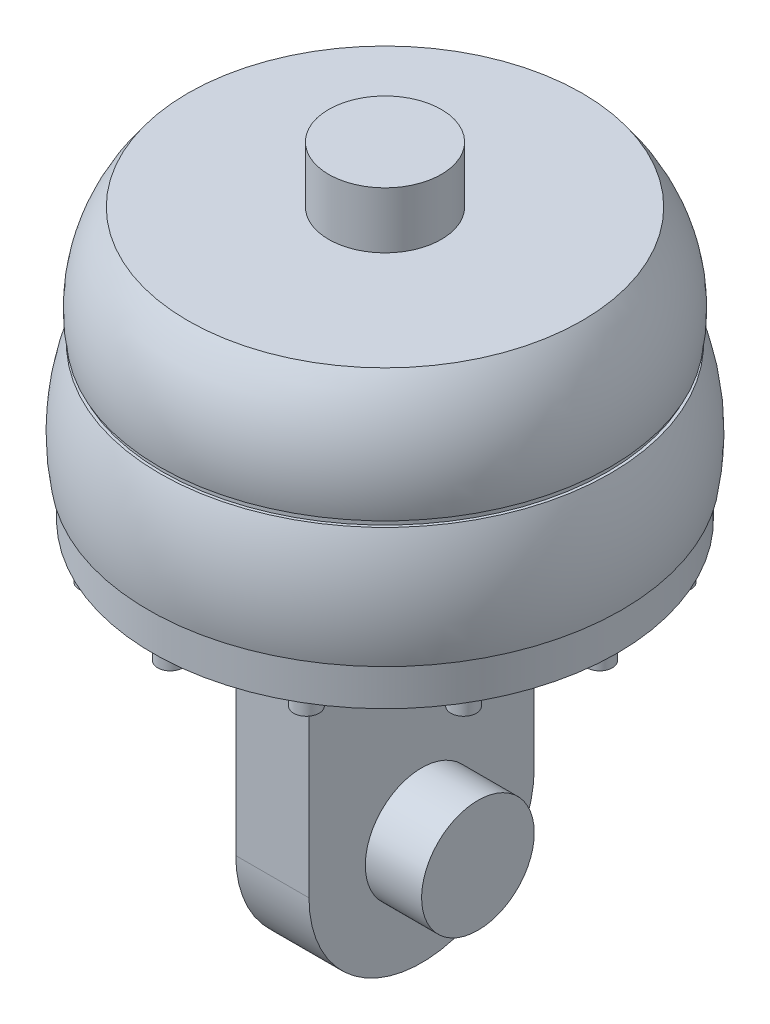
SolidWorks part; units mm, degrees
material "Cast Alloy Steel"
ref_plane "Front Plane" through (0, 0, 0) normal (0, 0, 1) x (1, 0, 0)
ref_plane "Top Plane" through (0, 0, 0) normal (0, 1, 0) x (1, 0, 0)
ref_plane "Right Plane" through (0, 0, 0) normal (1, 0, 0) x (0, 0, -1)
sketch "Sketch1" plane through (0, 0, 0) normal (0, 0, 1) x (1, 0, 0)
  line L0 (0, 0) -> (-35, 0)
  line L1 (0, 0) -> (0, -20)
  line L2 (0, -20) -> (-40, -20)
  arc A0 (-35, 0) -> (-40, -20) centre (-15.404, -15.524) ccw
  dimension "D4" = 25
  dimension "D1" = 35
  dimension "D2" = 20
  dimension "D3" = 40
revolve "Revolve1" add sketch "Sketch1" angle 360 about L1
sketch "Sketch2" plane through (0, -20, 0) normal (0, -1, 0) x (1, 0, 0)
  circle A0 centre (0, 0) radius 39.5
  dimension "D1" = 79
extrude "Boss-Extrude1" add sketch "Sketch2" along normal blind 1
sketch "Sketch4" plane through (0, 0, 0) normal (0, 0, 1) x (1, 0, 0)
  line L0 (0, -21) -> (0, -41)
  line L2 (-39.5, -21) -> (39.5, -21) construction
  line L3 (0, -21) -> (-40, -21)
  line L4 (0, -41) -> (-42, -41)
  arc A0 (-40, -21) -> (-42, -41) centre (-5.5677, -34.5432) ccw
  dimension "D4" = 37
  dimension "D1" = 40
  dimension "D2" = 20
  dimension "D3" = 42
revolve "Revolve2" add sketch "Sketch4" angle 360 about L0
sketch "Sketch5" plane through (0, -41, 0) normal (0, -1, 0) x (1, 0, 0)
  circle A0 centre (0, 0) radius 41.25
  dimension "D1" = 82.5
extrude "Boss-Extrude2" add sketch "Sketch5" along normal blind 7
sketch "Sketch6" plane through (0, -48, 0) normal (0, -1, 0) x (1, 0, 0)
  circle A0 centre (0, 0) radius 35
  dimension "D1" = 70
extrude "Boss-Extrude3" add sketch "Sketch6" along normal blind 3
sketch "Sketch7" plane through (0, -48, 0) normal (0, -1, 0) x (-1, 0, 0)
  line L0 (-35, 0) -> (-41.25, 0)
  circle A0 centre (0, 0) radius 35 construction
  circle A1 centre (0, 0) radius 35 construction
  circle A2 centre (0, 0) radius 41.25 construction
  circle A3 centre (-38.125, 0) radius 2.25
  dimension "D1" = 4.5
extrude "Boss-Extrude4" add sketch "Sketch7" along normal blind 2.7 contours L0 A3 | L0 A3
sketch "Sketch8" plane through (0, -50.7, 0) normal (0, -1, 0) x (1, 0, 0)
  circle A2 centre (38.125, 0) radius 1.25
  circle A3 centre (38.125, 0) radius 1.25
  dimension "D1" = 1
extrude "Cut-Extrude1" cut sketch "Sketch8" against normal blind 0.7
pattern_circular "CirPattern1" count 12 over 360 about axis through (0, 0, 0) along (0, 1, 0) of "Cut-Extrude1", "Boss-Extrude4"
sketch "Sketch9" plane through (0, -51, 0) normal (0, -1, 0) x (1, 0, 0)
  line L1 (6.5, 20) -> (-6.5, 20)
  line L2 (6.5, 20) -> (6.5, -20)
  line L3 (6.5, -20) -> (-6.5, -20)
  line L4 (-6.5, 20) -> (-6.5, -20)
  line L5 (6.5, 20) -> (-6.5, -20) construction
  line L6 (6.5, -20) -> (-6.5, 20) construction
  point P0 (0, 0)
  dimension "D1" = 13
  dimension "D2" = 40
extrude "Boss-Extrude5" add sketch "Sketch9" along normal blind 42
sketch "Sketch12" plane through (6.5, 0, 0) normal (1, 0, 0) x (0, 0, -1)
  line L0 (20, -93) -> (-20, -93) construction
  line L1 (20, -93) -> (-20, -93)
  arc A0 (-20, -93) -> (20, -93) centre (0, -93) ccw
extrude "Boss-Extrude7" add sketch "Sketch12" against normal up to surface (13 mm away) up to face at (-6.5, -72, 0)
sketch "Sketch13" plane through (6.5, 0, 0) normal (1, 0, 0) x (0, 0, -1)
  circle A0 centre (0, -93) radius 10
  dimension "D1" = 20
extrude "Boss-Extrude8" add sketch "Sketch13" along normal blind 10
sketch "Sketch14" plane through (0, 0, 0) normal (0, 1, 0) x (1, 0, 0)
  circle A0 centre (0, 0) radius 10
  dimension "D1" = 20
extrude "Boss-Extrude9" add sketch "Sketch14" along normal blind 10
